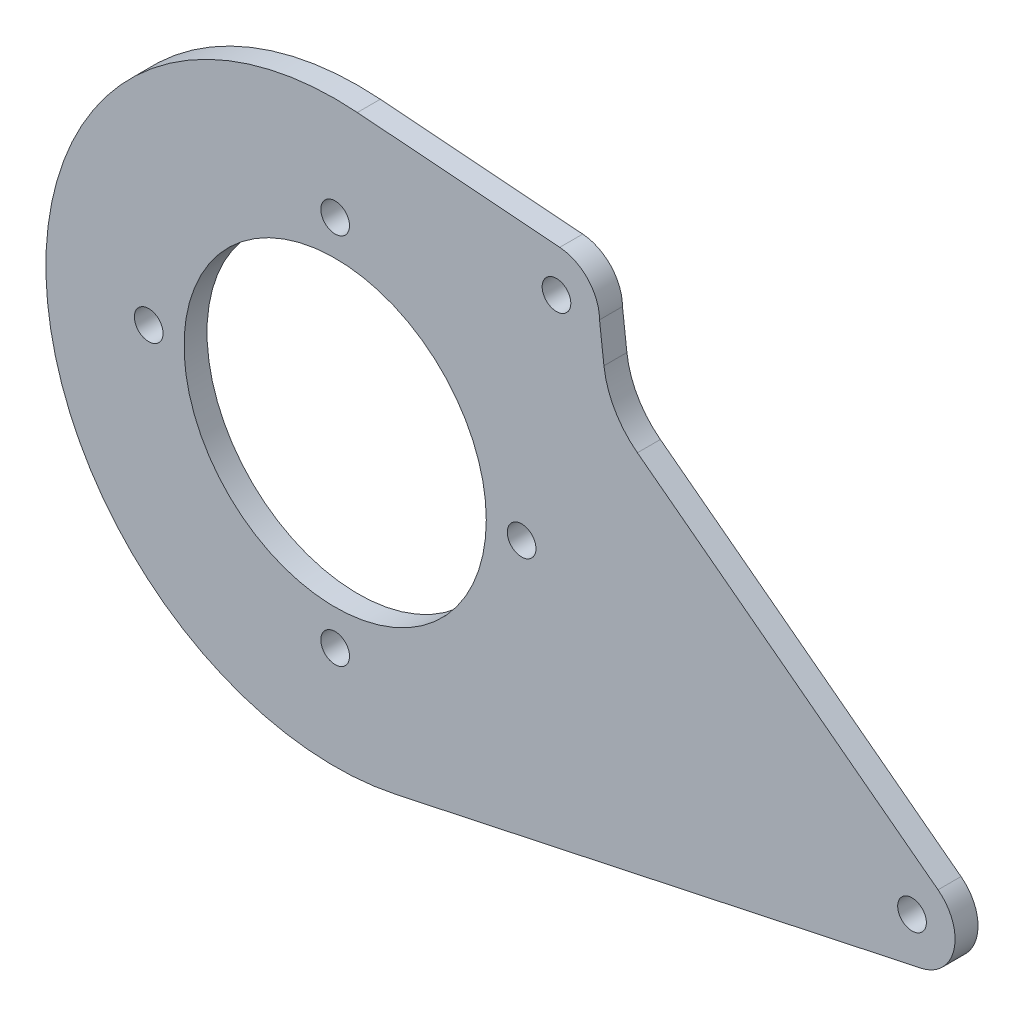
SolidWorks part; units mm, degrees
ref_plane "Front Plane" through (0, 0, 0) normal (0, 0, 1) x (1, 0, 0)
ref_plane "Top Plane" through (0, 0, 0) normal (0, 1, 0) x (1, 0, 0)
ref_plane "Right Plane" through (0, 0, 0) normal (1, 0, 0) x (0, 0, -1)
sketch "Sketch2" plane through (0, 0, 0) normal (0, 0, 1) x (1, 0, 0)
  line L3 (26.7128, -125.1816) -> (259.2067, -75.5692)
  line L4 (-465.3966, 682.9035) -> (262.1484, -78.6484) construction
  line L5 (9.8051, 127.6239) -> (99.3807, 120.742)
  line L6 (133.7246, 59.1995) -> (266.7532, -41.763)
  line L8 (118.9161, 85.1223) -> (116.9714, 101.748)
  circle A1 centre (0, 0) radius 66.87
  arc A2 (65.6, 0) -> (-65.6, 0) centre (0, 0) ccw construction
  circle A3 centre (0, 82.5) radius 6.35
  circle A4 centre (-82.5, 0) radius 6.35
  circle A5 centre (0, -82.5) radius 6.35
  circle A6 centre (82.5, 0) radius 6.35
  arc A10 (9.8051, 127.6239) -> (26.7128, -125.1816) centre (0, 0) ccw
  circle A11 centre (255.2365, -56.9375) radius 6.35
  arc A12 (259.2067, -75.5692) -> (266.7532, -41.763) centre (255.2365, -56.9375) ccw
  circle A13 centre (97.9214, 101.748) radius 6.35
  arc A14 (116.9714, 101.748) -> (99.3807, 120.742) centre (97.9214, 101.748) ccw
  arc A16 (17.4142, -126.8099) -> (48.3238, -118.5277) centre (0, 0) ccw construction
  arc A17 (133.7246, 59.1995) -> (118.9161, 85.1223) centre (156.7581, 89.5486) cw
  point P0 (0, 0)
  point P7 (0, 0)
  point P24 (0, 0)
  point P27 (0, 0)
  dimension "D3" = 1.27
  dimension "D4" = 12.7
  dimension "D5" = 12.7
  dimension "D1" = 12.7
  dimension "D2" = 12.7
  dimension "D6" = 38.1
extrude "Boss-Extrude1" add sketch "Sketch2" along normal blind 10.16
